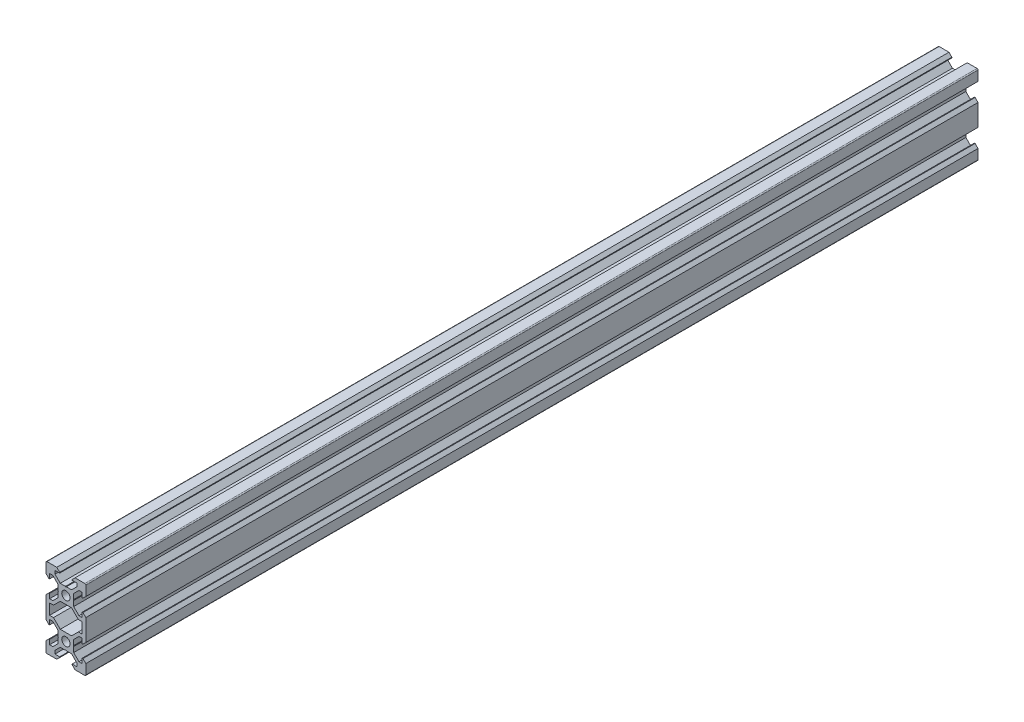
SolidWorks part; units mm, degrees
material "6061-T6 (SS)"
ref_plane "Front Plane" through (0, 0, 0) normal (0, 0, 1) x (1, 0, 0)
ref_plane "Top Plane" through (0, 0, 0) normal (0, 1, 0) x (1, 0, 0)
ref_plane "Right Plane" through (0, 0, 0) normal (1, 0, 0) x (0, 0, -1)
sketch "Sketch1" plane through (0, 0, 0) normal (0, 0, 1) x (1, 0, 0)
  line L0 (0, 0) -> (10, 0) construction
  line L1 (9.5, -20) -> (-9.5, -20)
  line L2 (10, -19.5) -> (10, 19.5)
  line L3 (9.5, 20) -> (-9.5, 20)
  line L4 (-10, -19.5) -> (-10, 19.5)
  line L5 (10, -20) -> (-10, 20) construction
  line L6 (10, 20) -> (-10, -20) construction
  circle A0 centre (0, 10) radius 2.1
  circle A1 centre (0, -10) radius 2.1
  arc A2 (-9.5, -20) -> (-10, -19.5) centre (-9.5, -19.5) cw
  arc A3 (9.5, -20) -> (10, -19.5) centre (9.5, -19.5) ccw
  arc A4 (10, 19.5) -> (9.5, 20) centre (9.5, 19.5) ccw
  arc A5 (-9.5, 20) -> (-10, 19.5) centre (-9.5, 19.5) ccw
  point P0 (0, 0)
  line B0 (0, 10) -> (0, 20) construction
  line B1 (0, 13.69) -> (-0.21, 13.9)
  line B2 (-0.21, 13.9) -> (-2.8393, 13.9)
  line B3 (-2.8393, 13.9) -> (-5.5, 16.5607)
  line B4 (-5.5, 16.5607) -> (-5.5, 18.2)
  line B5 (-5.5, 18.2) -> (-3.125, 18.2)
  line B6 (-3.125, 18.2) -> (-3.125, 18.545)
  line B7 (-3.125, 18.545) -> (-4.58, 20)
  line B8 (-4.58, 20) -> (4.58, 20)
  line B9 (0, 10) -> (-5.9132, 15.9132) construction
  line B10 (3.125, 18.545) -> (4.58, 20)
  line B11 (3.125, 18.2) -> (3.125, 18.545)
  line B12 (5.5, 18.2) -> (3.125, 18.2)
  line B13 (5.5, 16.5607) -> (5.5, 18.2)
  line B14 (2.8393, 13.9) -> (5.5, 16.5607)
  line B15 (0.21, 13.9) -> (2.8393, 13.9)
  line B16 (0, 13.69) -> (0.21, 13.9)
  line B17 (0, 10) -> (-10, 10) construction
  line B18 (-3.69, 10) -> (-3.9, 9.79)
  line B19 (-3.9, 9.79) -> (-3.9, 7.1607)
  line B20 (-3.9, 7.1607) -> (-6.5607, 4.5)
  line B21 (-6.5607, 4.5) -> (-8.2, 4.5)
  line B22 (-8.2, 4.5) -> (-8.2, 6.875)
  line B23 (-8.2, 6.875) -> (-8.545, 6.875)
  line B24 (-8.545, 6.875) -> (-10, 5.42)
  line B25 (-10, 5.42) -> (-10, 14.58)
  line B26 (0, 10) -> (-5.9132, 4.0868) construction
  line B27 (-8.545, 13.125) -> (-10, 14.58)
  line B28 (-8.2, 13.125) -> (-8.545, 13.125)
  line B29 (-8.2, 15.5) -> (-8.2, 13.125)
  line B30 (-6.5607, 15.5) -> (-8.2, 15.5)
  line B31 (-3.9, 12.8393) -> (-6.5607, 15.5)
  line B32 (-3.9, 10.21) -> (-3.9, 12.8393)
  line B33 (-3.69, 10) -> (-3.9, 10.21)
  line B34 (0, -10) -> (-10, -10) construction
  line B35 (-3.69, -10) -> (-3.9, -10.21)
  line B36 (-3.9, -10.21) -> (-3.9, -12.8393)
  line B37 (-3.9, -12.8393) -> (-6.5607, -15.5)
  line B38 (-6.5607, -15.5) -> (-8.2, -15.5)
  line B39 (-8.2, -15.5) -> (-8.2, -13.125)
  line B40 (-8.2, -13.125) -> (-8.545, -13.125)
  line B41 (-8.545, -13.125) -> (-10, -14.58)
  line B42 (-10, -14.58) -> (-10, -5.42)
  line B43 (0, -10) -> (-5.9132, -15.9132) construction
  line B44 (-8.545, -6.875) -> (-10, -5.42)
  line B45 (-8.2, -6.875) -> (-8.545, -6.875)
  line B46 (-8.2, -4.5) -> (-8.2, -6.875)
  line B47 (-6.5607, -4.5) -> (-8.2, -4.5)
  line B48 (-3.9, -7.1607) -> (-6.5607, -4.5)
  line B49 (-3.9, -9.79) -> (-3.9, -7.1607)
  line B50 (-3.69, -10) -> (-3.9, -9.79)
  line B51 (0, -10) -> (0, -20) construction
  line B52 (0, -13.69) -> (0.21, -13.9)
  line B53 (0.21, -13.9) -> (2.8393, -13.9)
  line B54 (2.8393, -13.9) -> (5.5, -16.5607)
  line B55 (5.5, -16.5607) -> (5.5, -18.2)
  line B56 (5.5, -18.2) -> (3.125, -18.2)
  line B57 (3.125, -18.2) -> (3.125, -18.545)
  line B58 (3.125, -18.545) -> (4.58, -20)
  line B59 (4.58, -20) -> (-4.58, -20)
  line B60 (0, -10) -> (5.9132, -15.9132) construction
  line B61 (-3.125, -18.545) -> (-4.58, -20)
  line B62 (-3.125, -18.2) -> (-3.125, -18.545)
  line B63 (-5.5, -18.2) -> (-3.125, -18.2)
  line B64 (-5.5, -16.5607) -> (-5.5, -18.2)
  line B65 (-2.8393, -13.9) -> (-5.5, -16.5607)
  line B66 (-0.21, -13.9) -> (-2.8393, -13.9)
  line B67 (0, -13.69) -> (-0.21, -13.9)
  line B68 (0, -10) -> (10, -10) construction
  line B69 (3.69, -10) -> (3.9, -9.79)
  line B70 (3.9, -9.79) -> (3.9, -7.1607)
  line B71 (3.9, -7.1607) -> (6.5607, -4.5)
  line B72 (6.5607, -4.5) -> (8.2, -4.5)
  line B73 (8.2, -4.5) -> (8.2, -6.875)
  line B74 (8.2, -6.875) -> (8.545, -6.875)
  line B75 (8.545, -6.875) -> (10, -5.42)
  line B76 (10, -5.42) -> (10, -14.58)
  line B77 (0, -10) -> (5.9132, -4.0868) construction
  line B78 (8.545, -13.125) -> (10, -14.58)
  line B79 (8.2, -13.125) -> (8.545, -13.125)
  line B80 (8.2, -15.5) -> (8.2, -13.125)
  line B81 (6.5607, -15.5) -> (8.2, -15.5)
  line B82 (3.9, -12.8393) -> (6.5607, -15.5)
  line B83 (3.9, -10.21) -> (3.9, -12.8393)
  line B84 (3.69, -10) -> (3.9, -10.21)
  line B85 (0, 10) -> (10, 10) construction
  line B86 (3.69, 10) -> (3.9, 10.21)
  line B87 (3.9, 10.21) -> (3.9, 12.8393)
  line B88 (3.9, 12.8393) -> (6.5607, 15.5)
  line B89 (6.5607, 15.5) -> (8.2, 15.5)
  line B90 (8.2, 15.5) -> (8.2, 13.125)
  line B91 (8.2, 13.125) -> (8.545, 13.125)
  line B92 (8.545, 13.125) -> (10, 14.58)
  line B93 (10, 14.58) -> (10, 5.42)
  line B94 (0, 10) -> (5.9132, 15.9132) construction
  line B95 (8.545, 6.875) -> (10, 5.42)
  line B96 (8.2, 6.875) -> (8.545, 6.875)
  line B97 (8.2, 4.5) -> (8.2, 6.875)
  line B98 (6.5607, 4.5) -> (8.2, 4.5)
  line B99 (3.9, 7.1607) -> (6.5607, 4.5)
  line B100 (3.9, 9.79) -> (3.9, 7.1607)
  line B101 (3.69, 10) -> (3.9, 9.79)
  line B102 (-8.2, -2.7) -> (-8.2, 2.7)
  line B103 (-8.2, 2.7) -> (-6.2393, 2.7)
  line B104 (-6.2393, 2.7) -> (-2.8393, 6.1)
  line B105 (-2.8393, 6.1) -> (2.8393, 6.1)
  line B106 (0, 6.1) -> (0, 0) construction
  line B107 (0, 0) -> (-8.2, 0) construction
  line B108 (6.2393, 2.7) -> (2.8393, 6.1)
  line B109 (8.2, 2.7) -> (6.2393, 2.7)
  line B110 (8.2, -2.7) -> (8.2, 2.7)
  line B111 (8.2, -2.7) -> (6.2393, -2.7)
  line B112 (6.2393, -2.7) -> (2.8393, -6.1)
  line B113 (-2.8393, -6.1) -> (2.8393, -6.1)
  line B114 (-6.2393, -2.7) -> (-2.8393, -6.1)
  line B115 (-8.2, -2.7) -> (-6.2393, -2.7)
  line B116 (0, 6.1) -> (0, 10) construction
  line B117 (0, 10) -> (-5.0927, 4.9073) construction
  dimension "D4" = 4.2
  dimension "D5" = 0.5
  dimension "D1" = 20
  dimension "D2" = 40
  dimension "D3" = 20
sketch_block_instance "V Slot 1-4"
sketch_block "V Slot 1" parameters "D1"=10, "D2"=11, "D3"=4.3, "D4"=1.8, "D5"=0.21, "D6"=45, "D7"=9.16, "D8"=1.5, "D9"=6.25
sketch_block_instance "V Slot 1-5"
sketch_block_instance "V Slot 1-6"
sketch_block_instance "V Slot 1-7"
sketch_block_instance "V Slot 1-8"
sketch_block_instance "V Slot 1-9"
sketch_block_instance "Center Cutout 1-1"
sketch_block "Center Cutout 1" parameters "D1"=5.4, "D2"=12.2, "D3"=8.2, "D4"=45, "D5"=10, "D6"=1.5
extrude "Boss-Extrude1" add sketch "Sketch1" along normal blind 448 contours B101 B86 B87 B88 B89 B90 B91 B92 L2 A4 L3 B10 B11 B12 B13 B14 B15 B16 B1 B2 B3 B4 B5 B6 B7 A5 L4 B27 B28 B29 B30 B31 B32 B33 B18 B19 B20 B21 B22 B23 B24 B44 B45 B46 B47 B48 B49 B50 B35
